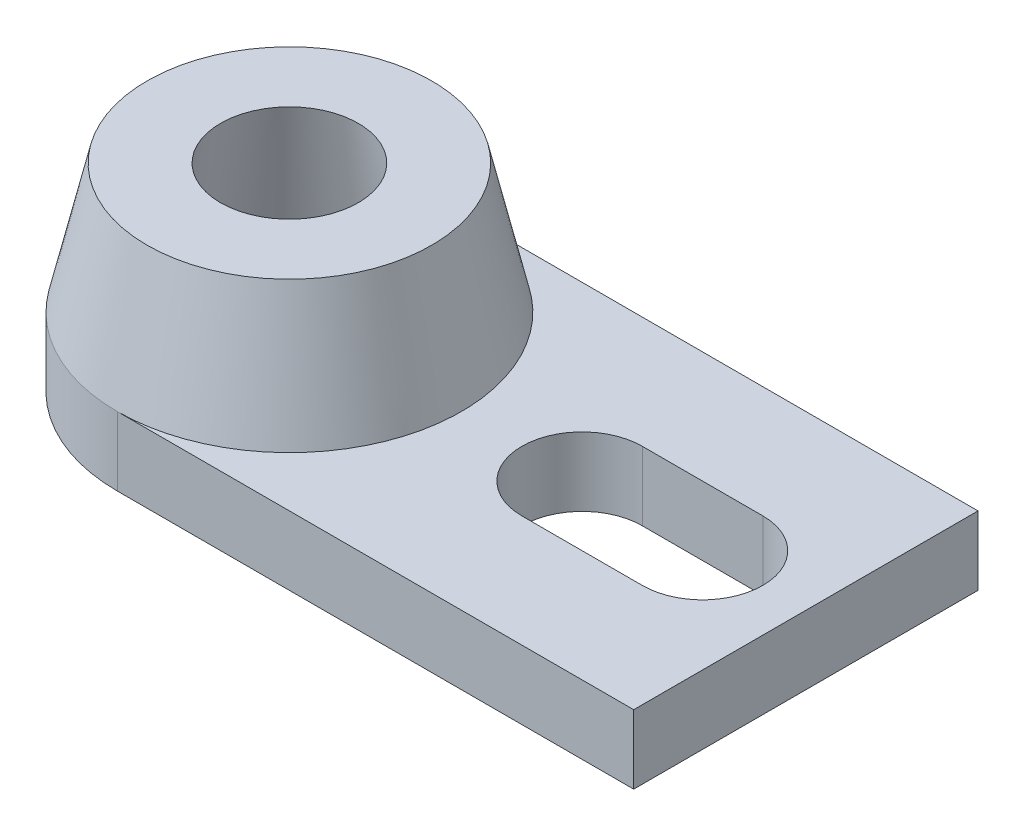
SolidWorks part; units mm, degrees
ref_plane "Alzado" through (0, 0, 0) normal (0, 0, 1) x (1, 0, 0)
ref_plane "Planta" through (0, 0, 0) normal (0, 1, 0) x (1, 0, 0)
ref_plane "Vista lateral" through (0, 0, 0) normal (1, 0, 0) x (0, 0, -1)
sketch "Croquis1" plane through (0, 0, 0) normal (0, 1, 0) x (1, 0, 0)
  line L1 (20, 0) -> (80, 0)
  line L3 (20, -40) -> (80, -40)
  line L4 (80, 0) -> (80, -40)
  line L5 (68, -13) -> (54, -13)
  line L6 (54, -27) -> (68, -27)
  arc A0 (68, -27) -> (68, -13) centre (68, -20) ccw
  arc A1 (54, -13) -> (54, -27) centre (54, -20) ccw
  arc A2 (20, 0) -> (20, -40) centre (20, -20) ccw
  dimension "D4" = 14
  dimension "D3" = 40
  dimension "D2" = 40
  dimension "D5" = 14
extrude "Saliente-Extruir1" add sketch "Croquis1" along normal blind 8
sketch "Croquis2" plane through (0, 8, 0) normal (0, 1, 0) x (1, 0, 0)
  line L0 (20, 0) -> (20, -40) construction
  circle A0 centre (20, -20) radius 20
extrude "Saliente-Extruir2" add sketch "Croquis2" along normal blind 15 draft 13
sketch "Croquis4" plane through (0, 23, 0) normal (0, 1, 0) x (1, 0, 0)
  line L0 (36.537, -20) -> (3.463, -20) construction
  circle A0 centre (20, -20) radius 16.537 construction
  circle A1 centre (20, -20) radius 8
  dimension "D1" = 16
extrude "Cortar-Extruir3" cut sketch "Croquis4" against normal blind 23 draft 10 draft outward yes
